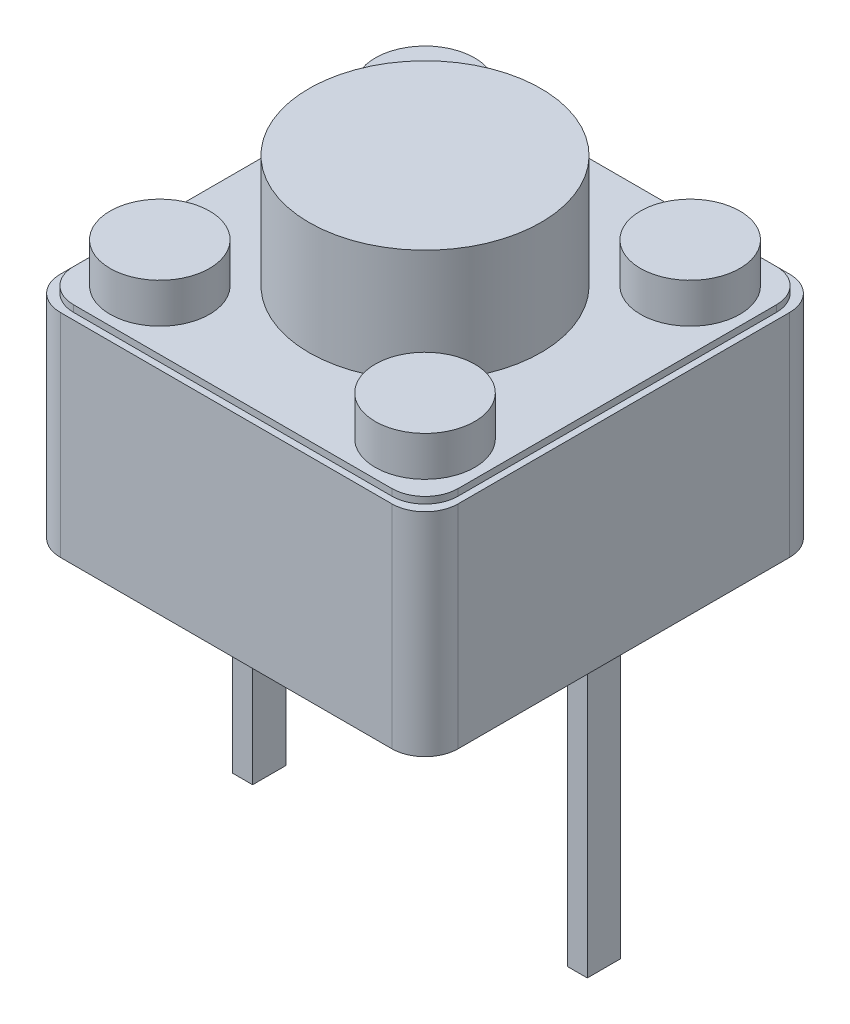
SolidWorks part; units mm, degrees
ref_plane "Plano frontal" through (0, 0, 0) normal (0, 0, 1) x (1, 0, 0)
ref_plane "Plano superior" through (0, 0, 0) normal (0, 1, 0) x (1, 0, 0)
ref_plane "Plano direito" through (0, 0, 0) normal (1, 0, 0) x (0, 0, -1)
sketch "Esboço1" plane through (0, 0, 0) normal (0, 1, 0) x (1, 0, 0)
  line L1 (-10, 10.2727) -> (-4, 10.2727)
  line L2 (-10, 10.2727) -> (-10, 4.2727)
  line L3 (-10, 4.2727) -> (-4, 4.2727)
  line L4 (-4, 10.2727) -> (-4, 4.2727)
  dimension "D1" = 6
  dimension "D2" = 6
extrude "Ressalto-extrusão1" add sketch "Esboço1" along normal blind 3.4
sketch "Esboço2" plane through (0, 3.4, 0) normal (0, 1, 0) x (1, 0, 0)
  circle A0 centre (-7, 7.2727) radius 1.75
  dimension "D1" = 3.5
extrude "Ressalto-extrusão2" add sketch "Esboço2" along normal blind 1.6 contours A0
sketch "Esboço3" plane through (0, 3.4, 0) normal (0, 1, 0) x (1, 0, 0)
  line L0 (-4, 10.2727) -> (-10, 10.2727) construction
  line L1 (-10, 10.2727) -> (-10, 4.2727) construction
  line L2 (-4, 4.2727) -> (-4, 10.2727) construction
  line L3 (-10, 4.2727) -> (-4, 4.2727) construction
  circle A0 centre (-9, 9.2727) radius 0.75
  circle A1 centre (-5, 9.2727) radius 0.75
  circle A2 centre (-9, 5.2727) radius 0.75
  circle A3 centre (-5, 5.2727) radius 0.75
  dimension "D1" = 1.5
  dimension "D2" = 1.5
  dimension "D3" = 1.5
  dimension "D4" = 1.5
  dimension "D5" = 1
  dimension "D6" = 1
  dimension "D7" = 1
  dimension "D8" = 1
  dimension "D9" = 1
  dimension "D10" = 1
  dimension "D11" = 1
  dimension "D12" = 1
extrude "Ressalto-extrusão3" add sketch "Esboço3" along normal blind 0.5
sketch "Esboço5" plane through (0, 0, 0) normal (0, -1, 0) x (1, 0, 0)
  line L4 (-4.6021, -7.2727) -> (-4.4521, -7.2727) construction
  line L6 (-9.35, -7.5227) -> (-9.65, -7.5227)
  line L7 (-9.35, -7.5227) -> (-9.35, -7.0227)
  line L8 (-9.35, -7.0227) -> (-9.65, -7.0227)
  line L9 (-9.65, -7.5227) -> (-9.65, -7.0227)
  line L12 (-4.3021, -7.5227) -> (-4.6021, -7.5227)
  line L13 (-4.3021, -7.5227) -> (-4.3021, -7.0227)
  line L14 (-4.3021, -7.0227) -> (-4.6021, -7.0227)
  line L15 (-4.6021, -7.5227) -> (-4.6021, -7.0227)
  dimension "D3" = 0.3
  dimension "D4" = 0.5
  dimension "D5" = 0.3
  dimension "D6" = 0.5
extrude "Ressalto-extrusão4" add sketch "Esboço5" along normal blind 4.27
sketch "Esboço6" plane through (0, 3.4, 0) normal (0, 1, 0) x (1, 0, 0)
  line L1 (-10, 4.2727) -> (-4, 4.2727)
  line L2 (-10, 4.2727) -> (-10, 10.2727)
  line L3 (-10, 10.2727) -> (-4, 10.2727)
  line L4 (-4, 4.2727) -> (-4, 10.2727)
extrude "Corte-extrusão1" cut sketch "Esboço6" against normal blind 0.6
sketch "Esboço7" plane through (0, 2.8, 0) normal (0, 1, 0) x (1, 0, 0)
  line L0 (-10, 4.2727) -> (-4, 4.2727) construction
  line L1 (-10, 10.2727) -> (-4, 10.2727)
  line L2 (-10, 10.2727) -> (-10, 4.2727)
  line L3 (-10, 4.2727) -> (-4, 4.2727)
  line L4 (-4, 10.2727) -> (-4, 4.2727)
  line L5 (-4, 4.2727) -> (-4, 10.2727) construction
extrude "Ressalto-extrusão5" add sketch "Esboço7" along normal blind 0.6
sketch "Esboço9" plane through (0, 3.4, 0) normal (0, 1, 0) x (1, 0, 0)
  line L1 (-10, 10.2727) -> (-4, 10.2727)
  line L2 (-10, 10.2727) -> (-10, 4.2727)
  line L3 (-10, 4.2727) -> (-4, 4.2727)
  line L4 (-4, 10.2727) -> (-4, 4.2727)
extrude "Corte-extrusão2" cut sketch "Esboço9" against normal blind 0.2
sketch "Esboço10" plane through (0, 3.2, 0) normal (0, 1, 0) x (1, 0, 0)
  line L0 (-10, 10.2727) -> (-10, 4.2727) construction
  line L1 (-9.9, 10.1727) -> (-4.1, 10.1727)
  line L2 (-9.9, 10.1727) -> (-9.9, 4.3727)
  line L3 (-9.9, 4.3727) -> (-4.1, 4.3727)
  line L4 (-4.1, 10.1727) -> (-4.1, 4.3727)
  line L5 (-4, 10.2727) -> (-10, 10.2727) construction
  line L6 (-4, 4.2727) -> (-4, 10.2727) construction
  line L7 (-10, 4.2727) -> (-4, 4.2727) construction
  dimension "D1" = 0.1
  dimension "D2" = 0.1
  dimension "D3" = 0.1
  dimension "D4" = 0.1
extrude "Ressalto-extrusão6" add sketch "Esboço10" along normal blind 0.1
fillet "Filete3" radius 0.5 4 edges at (-9.9, 3.25, -10.1727) (-9.9, 3.25, -4.3727) (-4.1, 3.25, -4.3727) (-4.1, 3.25, -10.1727)
fillet "Filete4" radius 0.5 4 edges at (-10, 1.6, -10.2727) (-4, 1.6, -10.2727) (-10, 1.6, -4.2727) (-4, 1.6, -4.2727)
sketch "Esboço12" plane through (0, 3.3, 0) normal (0, 1, 0) x (1, 0, 0)
  circle A0 centre (-7, 7.2727) radius 1.75
  circle A1 centre (-9, 9.2727) radius 0.7591
  circle A2 centre (-5, 9.2727) radius 0.75
  circle A3 centre (-5, 5.2727) radius 0.75
  circle A4 centre (-9, 5.2727) radius 0.75
extrude "Ressalto-extrusão7" add sketch "Esboço12" along normal blind 0.5
